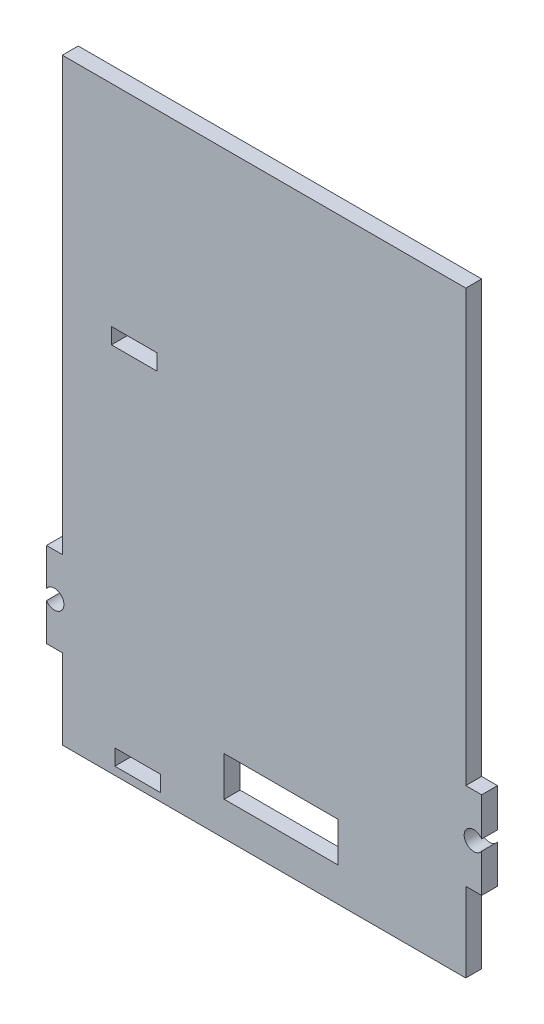
SolidWorks part; units mm, degrees
ref_plane "Front Plane" through (0, 0, 0) normal (0, 0, 1) x (1, 0, 0)
ref_plane "Top Plane" through (0, 0, 0) normal (0, 1, 0) x (1, 0, 0)
ref_plane "Right Plane" through (0, 0, 0) normal (1, 0, 0) x (0, 0, -1)
sketch "Sketch1" plane through (0, 0, 0) normal (0, 0, 1) x (1, 0, 0)
  line L1 (0, 0) -> (87, 0)
  line L2 (0, 0) -> (0, -44.45)
  line L3 (0, -44.45) -> (87, -44.45)
  line L4 (87, 0) -> (87, -44.45)
  line L5 (22.8034, -39.685) -> (13.6607, -39.685)
  line L6 (22.8034, -39.685) -> (22.8034, -42.86)
  line L7 (22.8034, -42.86) -> (13.6607, -42.86)
  line L8 (13.6607, -39.685) -> (13.6607, -42.86)
  dimension "D1" = 44.45
  dimension "D2" = 87
  dimension "D3" = 1.59
  dimension "D4" = 3.175
extrude "Boss-Extrude1" add sketch "Sketch1" along normal blind 3.175
sketch "Sketch2" plane through (0, 0, 0) normal (0, 0, -1) x (-1, 0, 0)
  line L1 (-87, 0) -> (-83.825, 0)
  line L2 (-87, 0) -> (-87, -11.14)
  line L3 (-87, -11.14) -> (-83.825, -11.14)
  line L4 (-83.825, 0) -> (-83.825, -11.14)
  dimension "D1" = 3.175
  dimension "D2" = 11.14
extrude "Cut-Extrude1" cut sketch "Sketch2" against normal through all
sketch "Sketch3" plane through (0, 0, 0) normal (0, 0, -1) x (-1, 0, 0)
  line L1 (-87, -44.45) -> (-83.825, -44.45)
  line L2 (-87, -44.45) -> (-87, -28.57)
  line L3 (-87, -28.57) -> (-83.825, -28.57)
  line L4 (-83.825, -44.45) -> (-83.825, -28.57)
  dimension "D1" = 15.88
  dimension "D2" = 3.175
extrude "Cut-Extrude2" cut sketch "Sketch3" against normal through all
sketch "Sketch6" plane through (0, 0, 0) normal (0, 0, -1) x (-1, 0, 0)
  line L0 (-87, -19.855) -> (-83.825, -19.855) construction
  line L1 (-87, -28.57) -> (-87, -11.14) construction
  circle A0 centre (-85.4125, -19.855) radius 1.905
  dimension "D1" = 3.81
  dimension "D2" = 1.5875
extrude "Cut-Extrude3" cut sketch "Sketch6" against normal through all
sketch "Sketch8" plane through (0, 0, 0) normal (0, 0, -1) x (-1, 0, 0)
  line L1 (0, 0) -> (-3.175, 0)
  line L2 (0, 0) -> (0, -11.469)
  line L3 (0, -11.469) -> (-3.175, -11.469)
  line L4 (-3.175, 0) -> (-3.175, -11.469)
  line L5 (0, -44.45) -> (-3.175, -44.45)
  line L6 (0, -44.45) -> (0, -28.467)
  line L7 (0, -28.467) -> (-3.175, -28.467)
  line L8 (-3.175, -44.45) -> (-3.175, -28.467)
  dimension "D1" = 3.175
  dimension "D2" = 3.175
extrude "Cut-Extrude4" cut sketch "Sketch8" against normal through all
sketch "Sketch10" plane through (0, 0, 0) normal (0, 0, -1) x (-1, 0, 0)
  line L0 (0, -19.968) -> (-1.5875, -19.968) construction
  line L1 (0, -11.469) -> (0, -28.467) construction
  circle A0 centre (-1.5875, -19.968) radius 1.905
  dimension "D1" = 3.81
extrude "Cut-Extrude5" cut sketch "Sketch10" against normal through all
sketch "Sketch12" plane through (0, 0, 0) normal (0, 1, 0) x (1, 0, 0)
  line L1 (83.825, 0) -> (3.175, 0)
  line L2 (83.825, 0) -> (83.825, -3.175)
  line L3 (83.825, -3.175) -> (3.175, -3.175)
  line L4 (3.175, 0) -> (3.175, -3.175)
extrude "Boss-Extrude2" add sketch "Sketch12" along normal blind 75
sketch "Sketch17" plane through (0, 0, 3.175) normal (0, 0, 1) x (1, 0, 0)
  line L0 (12.9917, -40.1734) -> (12.9917, 29.7566) construction
sketch "Sketch18" plane through (0, 0, 3.175) normal (0, 0, 1) x (1, 0, 0)
  line L1 (12.9917, 29.7566) -> (22.1317, 29.7566)
  line L2 (12.9917, 29.7566) -> (12.9917, 32.9366)
  line L3 (12.9917, 32.9366) -> (22.1317, 32.9366)
  line L4 (22.1317, 29.7566) -> (22.1317, 32.9366)
  dimension "D1" = 9.14
  dimension "D2" = 3.18
extrude "Cut-Extrude6" cut sketch "Sketch18" against normal blind 3.18
sketch "Sketch19" plane through (0, 0, 3.175) normal (0, 0, 1) x (1, 0, 0)
  line L1 (35.5298, -37.6501) -> (58.3167, -37.6501)
  line L2 (35.5298, -37.6501) -> (35.5298, -29.7416)
  line L3 (35.5298, -29.7416) -> (58.3167, -29.7416)
  line L4 (58.3167, -37.6501) -> (58.3167, -29.7416)
extrude "Cut-Extrude7" cut sketch "Sketch19" against normal blind 3.18
